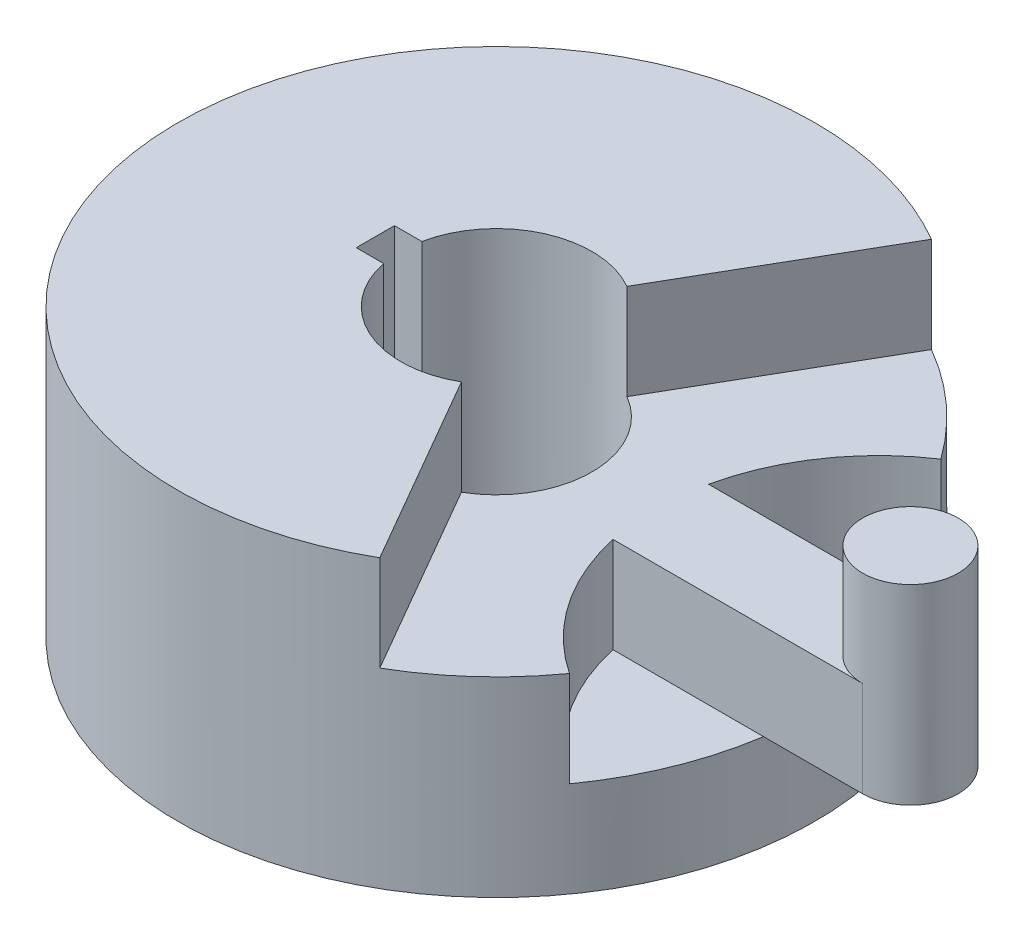
SolidWorks part; units mm, degrees
ref_plane "Front Plane" through (0, 0, 0) normal (0, 0, 1) x (1, 0, 0)
ref_plane "Top Plane" through (0, 0, 0) normal (0, 1, 0) x (1, 0, 0)
ref_plane "Right Plane" through (0, 0, 0) normal (1, 0, 0) x (0, 0, -1)
sketch "Sketch1" plane through (0, 0, 0) normal (0, 1, 0) x (1, 0, 0)
  line L0 (0, 0) -> (60, 0) construction
  arc A0 (40.625, 29.1481) -> (40.625, -29.1481) centre (0, 0) ccw
  circle A1 centre (0, 0) radius 15
  arc A4 (40.625, 29.1481) -> (40.625, -29.1481) centre (60, 0) ccw
  dimension "D1" = 100
  dimension "D2" = 30
  dimension "D3" = 70
  dimension "D4" = 60
extrude "Boss-Extrude6" add sketch "Sketch1" along normal mid plane 30 contours A1
sketch "Sketch4" plane through (0, 0, 0) normal (0, 1, 0) x (1, 0, 0)
  line L0 (65, 7.5) -> (25.813, 7.5)
  line L1 (65, -7.5) -> (25.813, -7.5)
  arc A0 (65, -7.5) -> (65, 7.5) centre (65, 0) ccw
  arc A1 (40.625, 29.1481) -> (40.625, -29.1481) centre (60, 0) ccw construction
  arc A2 (25.813, 7.5) -> (25.813, -7.5) centre (60, 0) ccw
  dimension "D1" = 15
  dimension "D2" = 65
extrude "Boss-Extrude7" add sketch "Sketch4" against normal blind 15
sketch "Sketch5" plane through (0, 15, 0) normal (0, 1, 0) x (1, 0, 0)
  circle A0 centre (65, 0) radius 7.5
  arc A1 (65, -7.5) -> (65, 7.5) centre (65, 0) ccw construction
extrude "Boss-Extrude8" add sketch "Sketch5" against normal blind 30
sketch "Sketch6" plane through (0, -15, 0) normal (0, -1, 0) x (1, 0, 0)
  circle A0 centre (0, 0) radius 50
  arc A1 (40.625, 29.1481) -> (40.625, -29.1481) centre (0, 0) ccw construction
extrude "Boss-Extrude9" add sketch "Sketch6" along normal blind 15
sketch "Sketch7" plane through (0, 15, 0) normal (0, 1, 0) x (1, 0, 0)
  line L0 (0, 0) -> (36.9872, 0) construction
  line L1 (0, 0) -> (25, -43.3013)
  line L2 (0, 0) -> (25, 43.3013)
  arc A0 (40.625, 29.1481) -> (40.625, -29.1481) centre (0, 0) ccw construction
  arc A2 (25, -43.3013) -> (40.625, -29.1481) centre (0, 0) ccw
  arc A4 (40.625, 29.1481) -> (40.625, -29.1481) centre (60, 0) ccw
  arc A5 (40.625, 29.1481) -> (40.625, -29.1481) centre (0, 0) ccw
  arc A6 (40.625, 29.1481) -> (40.625, -29.1481) centre (60, 0) ccw
  arc A7 (40.625, 29.1481) -> (25, 43.3013) centre (0, 0) ccw
  dimension "D1" = 60
  dimension "D2" = 0
extrude "Cut-Extrude1" cut sketch "Sketch7" against normal blind 15
sketch "Sketch8" plane through (0, -15, 0) normal (0, 1, 0) x (1, 0, 0)
  circle A1 centre (0, 0) radius 15
  circle A2 centre (0, 0) radius 15
  dimension "D1" = 0
extrude "Cut-Extrude2" cut sketch "Sketch8" against normal through all
sketch "Sketch9" plane through (0, 15, 0) normal (0, 1, 0) x (1, 0, 0)
  line L0 (0, 0) -> (-15, 0) construction
  line L6 (-19, 3) -> (-11, 3)
  line L7 (-19, 3) -> (-19, -3)
  line L8 (-19, -3) -> (-11, -3)
  line L9 (-11, 3) -> (-11, -3)
  line L10 (-15, -3) -> (-15, 3) construction
  line L11 (-19, 0) -> (-11, 0) construction
  arc A1 (7.5, 12.9904) -> (7.5, -12.9904) centre (0, 0) ccw construction
  dimension "D1" = 8
  dimension "D2" = 6
extrude "Cut-Extrude3" cut sketch "Sketch9" against normal through all
